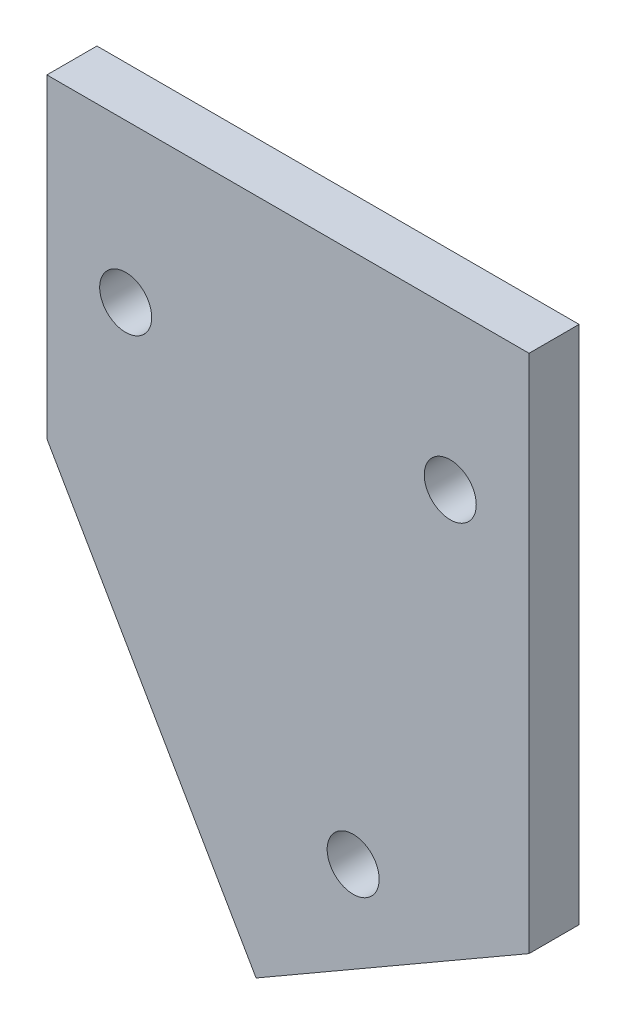
SolidWorks part; units mm, degrees
ref_plane "Front Plane" through (0, 0, 0) normal (0, 0, 1) x (1, 0, 0)
ref_plane "Top Plane" through (0, 0, 0) normal (0, 1, 0) x (1, 0, 0)
ref_plane "Right Plane" through (0, 0, 0) normal (1, 0, 0) x (0, 0, -1)
sketch "Sketch1" plane through (0, 0, 0) normal (0, 0, 1) x (1, 0, 0)
  line L0 (0, 0) -> (13.2735, -22.9904)
  line L1 (13.2735, -22.9904) -> (30.594, -12.9904)
  line L2 (30.594, -12.9904) -> (30.594, 20)
  line L3 (30.594, 20) -> (0, 20)
  line L4 (0, 20) -> (0, 0)
  line L5 (0, 0) -> (30.594, 0) construction
  line L6 (30.594, -12.9904) -> (23.094, 0) construction
  line L7 (0, 10) -> (30.594, 10) construction
  line L8 (21.9338, -17.9904) -> (19.4338, -13.6603) construction
  circle A0 centre (19.4338, -13.6603) radius 1.65
  circle A1 centre (5, 10) radius 1.65
  circle A2 centre (25.594, 10) radius 1.65
  dimension "D3" = 3.3
  dimension "D1" = 20
  dimension "D2" = 30
  dimension "D4" = 5
  dimension "D5" = 5
  dimension "D6" = 5
  dimension "D7" = 15
extrude "Boss-Extrude1" add sketch "Sketch1" along normal blind 3.175
